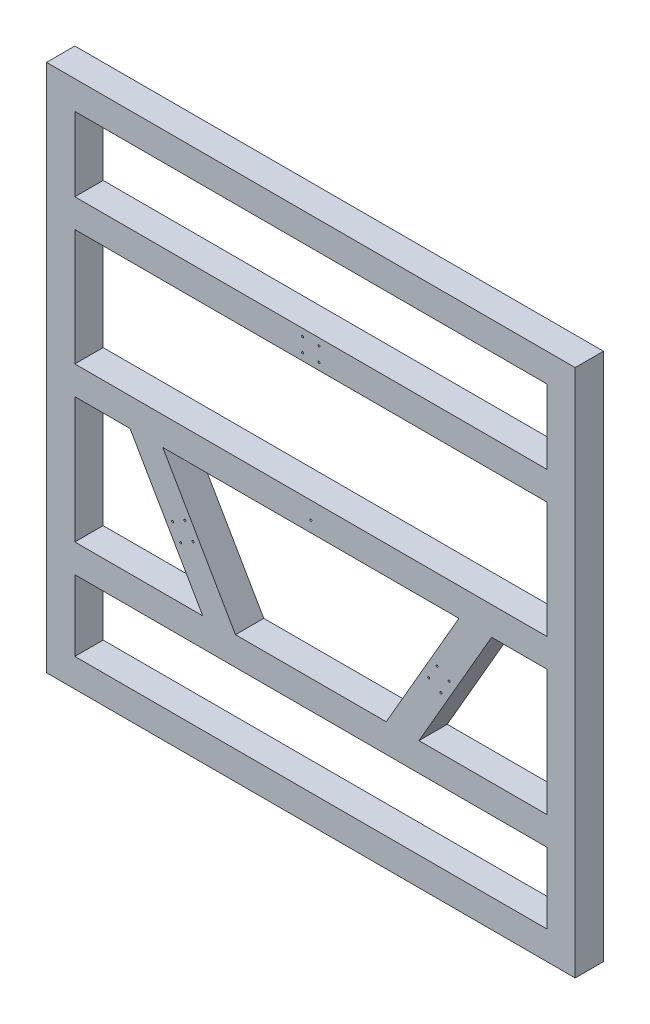
SolidWorks part; units mm, degrees
material "1060-H14"
ref_plane "Alzado" through (0, 0, 0) normal (0, 0, 1) x (1, 0, 0)
ref_plane "Planta" through (0, 0, 0) normal (0, 1, 0) x (1, 0, 0)
ref_plane "Vista lateral" through (0, 0, 0) normal (1, 0, 0) x (0, 0, -1)
sketch "Croquis1" plane through (0, 0, 0) normal (0, 0, 1) x (1, 0, 0)
  line L0 (0, 0) -> (0, 470) construction
  line L1 (0, 0) -> (-407.0319, -235) construction
  line L2 (0, 0) -> (407.0319, -235) construction
  line L3 (-750, 470) -> (750, 470) construction
  line L4 (291.5619, -435) -> (522.502, -35) construction
  line L5 (-522.502, -35) -> (-291.5619, -435) construction
  line L6 (-750, -235) -> (750, -235) construction
  line L7 (-750, -750) -> (750, -750)
  line L8 (-750, -750) -> (-750, 750)
  line L9 (-750, 750) -> (750, 750)
  line L10 (750, -750) -> (750, 750)
  line L11 (-750, -750) -> (750, 750) construction
  line L12 (-750, 750) -> (750, -750) construction
  line L13 (-750, -435) -> (750, -435)
  line L14 (-750, -35) -> (750, -35)
  line L15 (-750, 515) -> (750, 515)
  line L16 (-750, 425) -> (750, 425)
  line L17 (-840, -840) -> (-840, 840)
  line L18 (-840, 840) -> (840, 840)
  line L19 (840, -840) -> (840, 840)
  line L20 (-840, -840) -> (840, -840)
  line L21 (-750, 55) -> (750, 55)
  line L22 (-750, -525) -> (750, -525)
  line L23 (-574.4635, -35) -> (-343.5234, -435)
  line L24 (-470.5405, -35) -> (-239.6004, -435)
  line L25 (574.4635, -35) -> (343.5234, -435)
  line L26 (470.5405, -35) -> (239.6004, -435)
  circle A0 centre (0, 0) radius 400 construction
  circle A1 centre (0, 0) radius 470 construction
  point P10 (0, 470)
  point P14 (407.0319, -235)
  point P17 (-407.0319, -235)
  point P22 (0, 470)
  dimension "D1" = 800
  dimension "D3" = 120
  dimension "D4" = 120
  dimension "D5" = 1500
  dimension "D6" = 1500
  dimension "D7" = 400
  dimension "D8" = 90
  dimension "D10" = 90
  dimension "D11" = 90
  dimension "D12" = 90
  dimension "D13" = 90
  dimension "D2" = 70
  dimension "D9" = 90
extrude "Saliente-Extruir1" add sketch "Croquis1" along normal blind 90 contours L17 L20 L19 L18 L10 L7 L8 L9 | L8 L16 L10 L15 | L21 L8 L14 L10 | L8 L22 L10 L13 | L24 L14 L23 L13 | L14 L26 L13 L25
hole_wizard "Taladro de margen para M61" positions "Croquis2" profile "Croquis3" hole size "M6" standard "ISO" end condition through all
sketch "Croquis2" plane through (0, 0, 90) normal (0, 0, 1) x (1, 0, 0)
  line L0 (0, -1000) -> (0, 49000) construction
  line L1 (-1000, 470) -> (49000, 470) construction
  circle A0 centre (0, 0) radius 470 construction
  point P0 (-26, 492.5)
  point P18 (26, 492.5)
  point P19 (26, 447.5)
  point P20 (-26, 447.5)
  point P29 (439.5175, -223.7333)
  point P30 (413.5175, -268.7667)
  point P31 (374.5464, -246.2667)
  point P32 (400.5464, -201.2333)
  point P33 (-413.5175, -268.7667)
  point P34 (-439.5175, -223.7333)
  point P35 (-400.5464, -201.2333)
  point P36 (-374.5464, -246.2667)
  point P37 (0, 0)
  dimension "D1" = 940
  dimension "D2" = 45
  dimension "D3" = 52
  dimension "D4" = 3
sketch "Croquis3" plane through (-26, 492.5, 90) normal (1, 0, 0) x (0, -1, 0)
  line L0 (0, 0) -> (0, 90)
  line L1 (0, 90) -> (3.2, 90)
  line L2 (3.2, 90) -> (3.2, 0)
  line L5 (3.2, 0) -> (0, 0)
  line L11 (0, -6.35) -> (0, 107.95) construction
  dimension "Diámetro de taladro hasta el siguiente" = 6.4
  dimension "Profundidad de taladro hasta el siguiente" = 90
